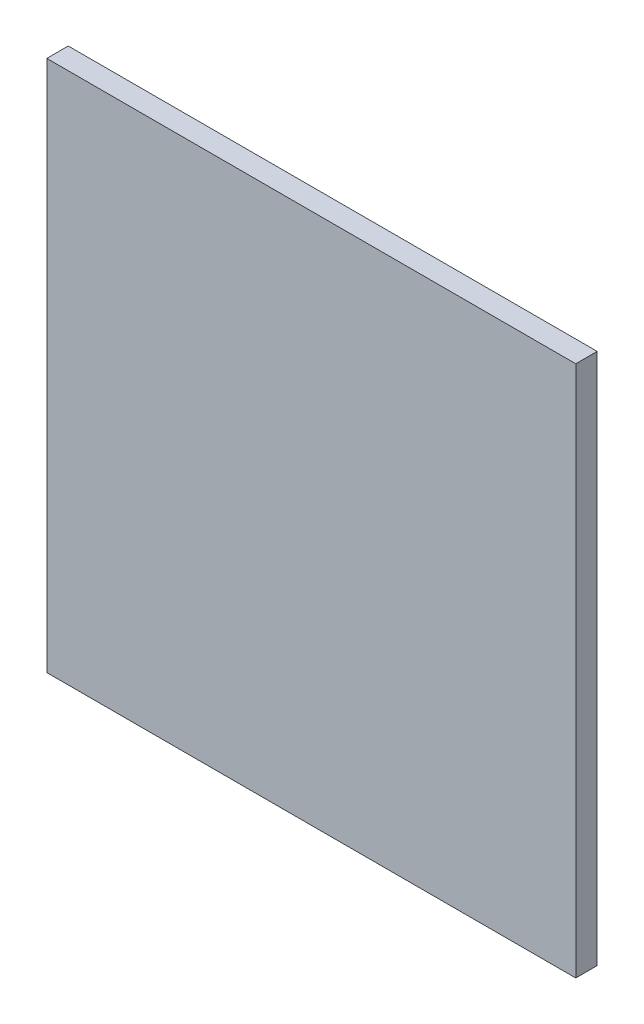
SolidWorks part; units mm, degrees
ref_plane "Front Plane" through (0, 0, 0) normal (0, 0, 1) x (1, 0, 0)
ref_plane "Top Plane" through (0, 0, 0) normal (0, 1, 0) x (1, 0, 0)
ref_plane "Right Plane" through (0, 0, 0) normal (1, 0, 0) x (0, 0, -1)
sketch "Sketch1" plane through (0, 0, 172.4071) normal (0, 0, 1) x (1, 0, 0)
  line L1 (-9.833, 239.7805) -> (138.167, 239.7805)
  line L2 (-9.833, 239.7805) -> (-9.833, 90.9462)
  line L3 (-9.833, 90.9462) -> (138.167, 90.9462)
  line L4 (138.167, 239.7805) -> (138.167, 90.9462)
  arc A2 (141.167, 168.5081) -> (141.167, 163.0529) centre (141.167, 165.7805) ccw construction
  arc A3 (-12.833, 163.0529) -> (-12.833, 168.5081) centre (-12.833, 165.7805) ccw construction
  arc A4 (33.9394, 242.7805) -> (39.3947, 242.7805) centre (36.667, 242.7805) ccw construction
  dimension "D1" = 3
  dimension "D2" = 3
  dimension "D3" = 3
extrude "Boss-Extrude1" add sketch "Sketch1" along normal blind 6
